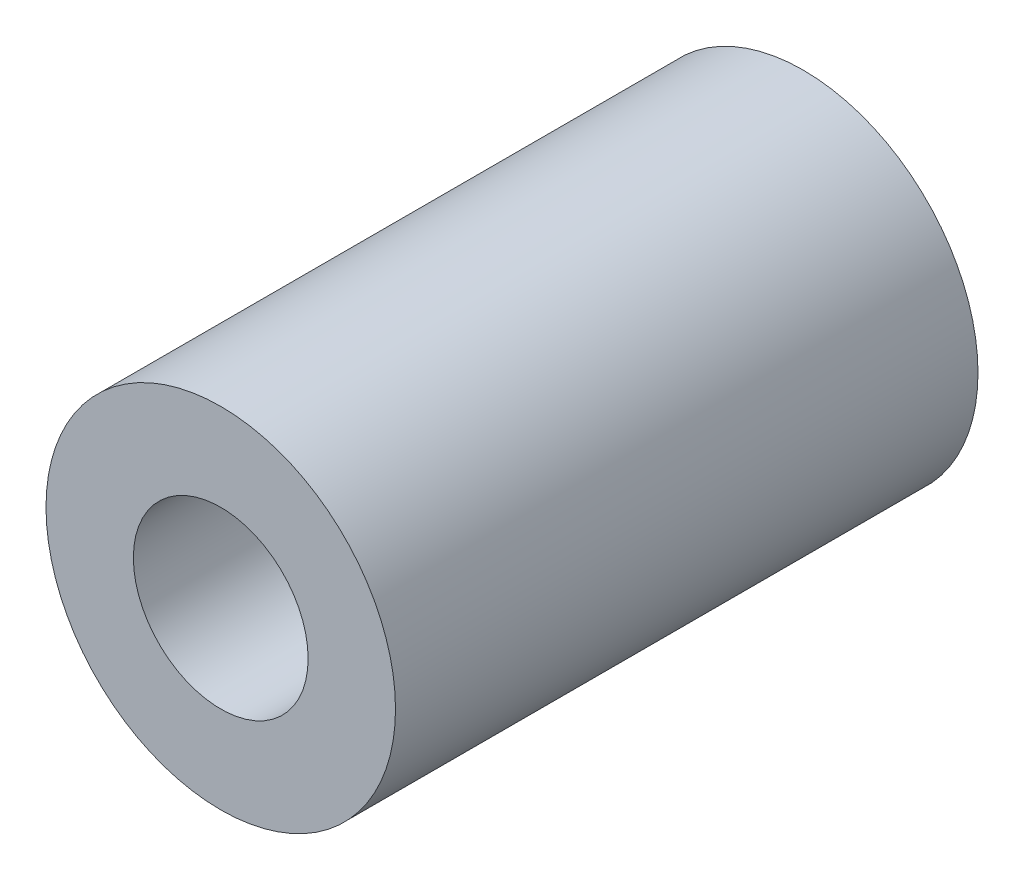
SolidWorks part; units mm, degrees
material "7075-O (SS)"
ref_plane "Płaszczyzna XY" through (0, 0, 0) normal (0, 0, 1) x (1, 0, 0)
ref_plane "Płaszczyzna XZ" through (0, 0, 0) normal (0, 1, 0) x (1, 0, 0)
ref_plane "Płaszczyzna YZ" through (0, 0, 0) normal (1, 0, 0) x (0, 0, -1)
sketch "Szkic1" plane through (0, 0, 0) normal (0, 0, 1) x (1, 0, 0)
  circle A0 centre (0, 0) radius 3
  circle A1 centre (0, 0) radius 1.5
  dimension "D1" = 3
  dimension "D2" = 6
extrude "Dodanie-wyciągnięcie1" add sketch "Szkic1" along normal blind 10
